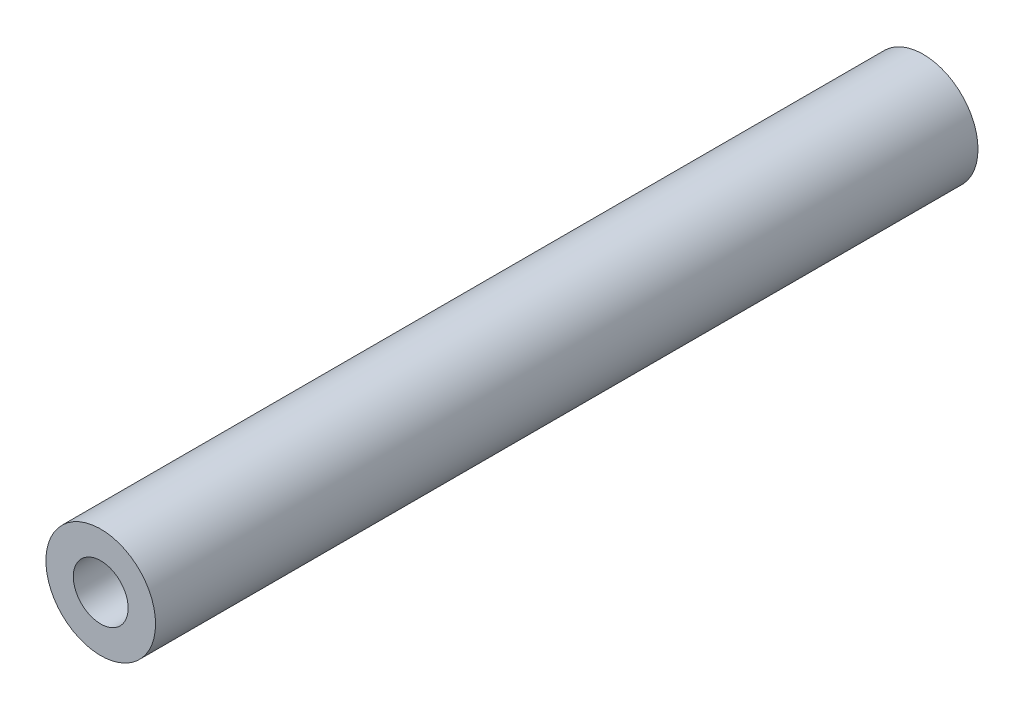
SolidWorks part; units mm, degrees
material "PTFE"
ref_plane "Front Plane" through (0, 0, 0) normal (0, 0, 1) x (1, 0, 0)
ref_plane "Top Plane" through (0, 0, 0) normal (0, 1, 0) x (1, 0, 0)
ref_plane "Right Plane" through (0, 0, 0) normal (1, 0, 0) x (0, 0, -1)
sketch "Sketch1" plane through (0, 0, 0) normal (0, 0, 1) x (1, 0, 0)
  circle A0 centre (0, 0) radius 1
  circle A1 centre (0, 0) radius 2
  dimension "D1" = 4
  dimension "D2" = 2
extrude "Boss-Extrude1" add sketch "Sketch1" along normal blind 30
